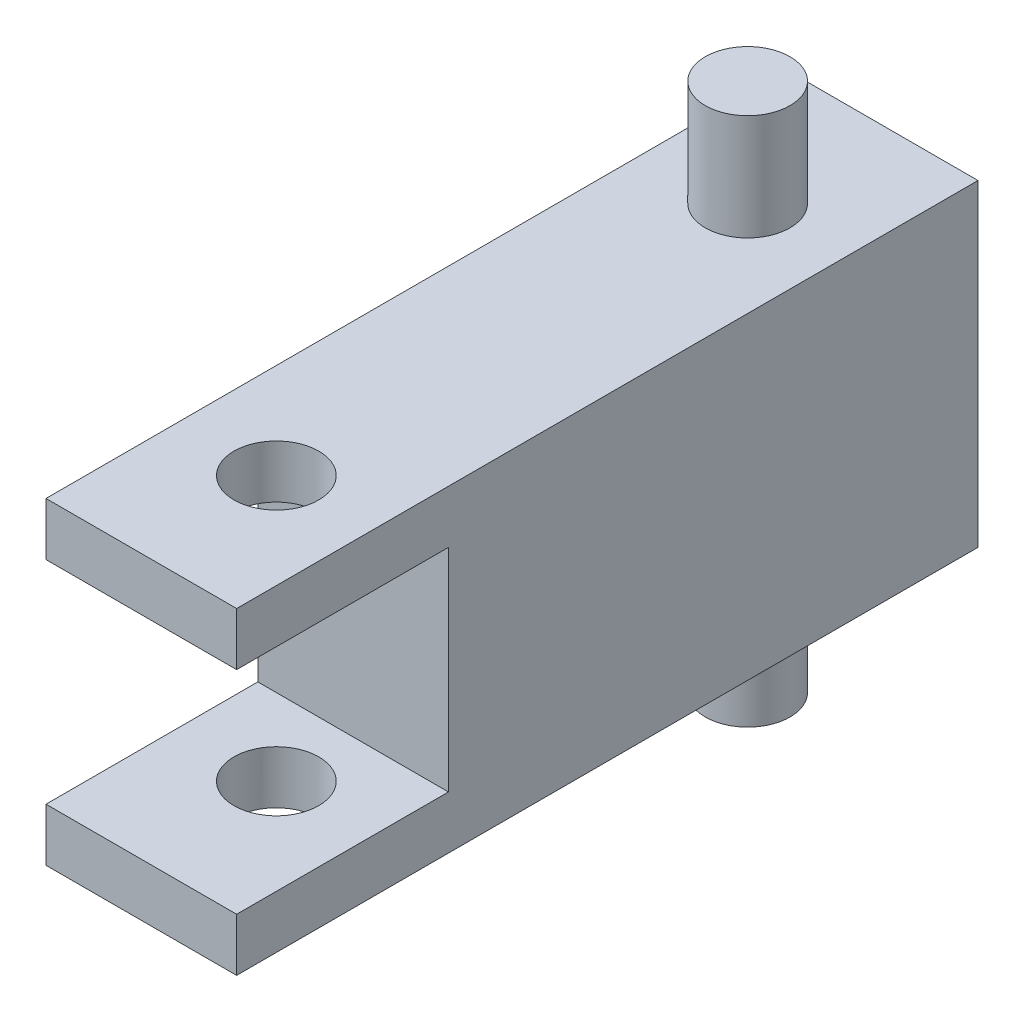
SolidWorks part; units mm, degrees
ref_plane "Plan de face" through (0, 0, 0) normal (0, 0, 1) x (1, 0, 0)
ref_plane "Plan de dessus" through (0, 0, 0) normal (0, 1, 0) x (1, 0, 0)
ref_plane "Plan de droite" through (0, 0, 0) normal (1, 0, 0) x (0, 0, -1)
sketch "Esquisse1" plane through (0, 0, 0) normal (0, 0, 1) x (1, 0, 0)
  line L1 (-9, 15) -> (9, 15)
  line L2 (-9, 15) -> (-9, -15)
  line L3 (-9, -15) -> (9, -15)
  line L4 (9, 15) -> (9, -15)
  line L5 (-9, 15) -> (9, -15) construction
  line L6 (-9, -15) -> (9, 15) construction
  point P0 (0, 0)
  dimension "D1" = 18
  dimension "D2" = 30
extrude "Boss.-Extru.1" add sketch "Esquisse1" along normal blind 70
sketch "Esquisse2" plane through (0, 15, 0) normal (0, 1, 0) x (1, 0, 0)
  line L0 (0, 0) -> (0, -12.3522) construction
  line L1 (9, 0) -> (-9, 0) construction
  circle A0 centre (0, -12.75) radius 4
  dimension "D2" = 8
  dimension "D1" = 12.75
extrude "Boss.-Extru.2" add sketch "Esquisse2" along normal blind 10
mirror "Symétrie1" about plane through (0, 0, 0) normal (0, 1, 0) of "Boss.-Extru.2"
ref_plane "Plan5" through (0, 0, 35) normal (0, 0, 1) x (1, 0, 0)
mirror "Symétrie2" about plane through (0, 0, 35) normal (0, 0, 1) of "Boss.-Extru.2"
sketch "Esquisse3" plane through (0, 25, 0) normal (0, 1, 0) x (1, 0, 0)
  circle A0 centre (0, -57.25) radius 4 construction
  circle A1 centre (0, -57.25) radius 4
extrude "Enlèv. mat.-Extru.1" cut sketch "Esquisse3" against normal blind 52
sketch "Esquisse4" plane through (9, 0, 0) normal (1, 0, 0) x (0, 0, -1)
  line L0 (-70, 0) -> (-41.6671, 0) construction
  line L1 (-70, -15) -> (-70, 15) construction
  line L2 (-70, 15) -> (0, 15) construction
  line L3 (-50, -10) -> (-70, -10)
  line L4 (-50, -10) -> (-50, 10)
  line L5 (-50, 10) -> (-70, 10)
  line L6 (-70, -10) -> (-70, 10)
  line L7 (-50, -10) -> (-70, 10) construction
  line L8 (-50, 10) -> (-70, -10) construction
  point P4 (-60, 0)
  dimension "D1" = 5
  dimension "D2" = 20
extrude "Enlèv. mat.-Extru.2" cut sketch "Esquisse4" against normal blind 52
